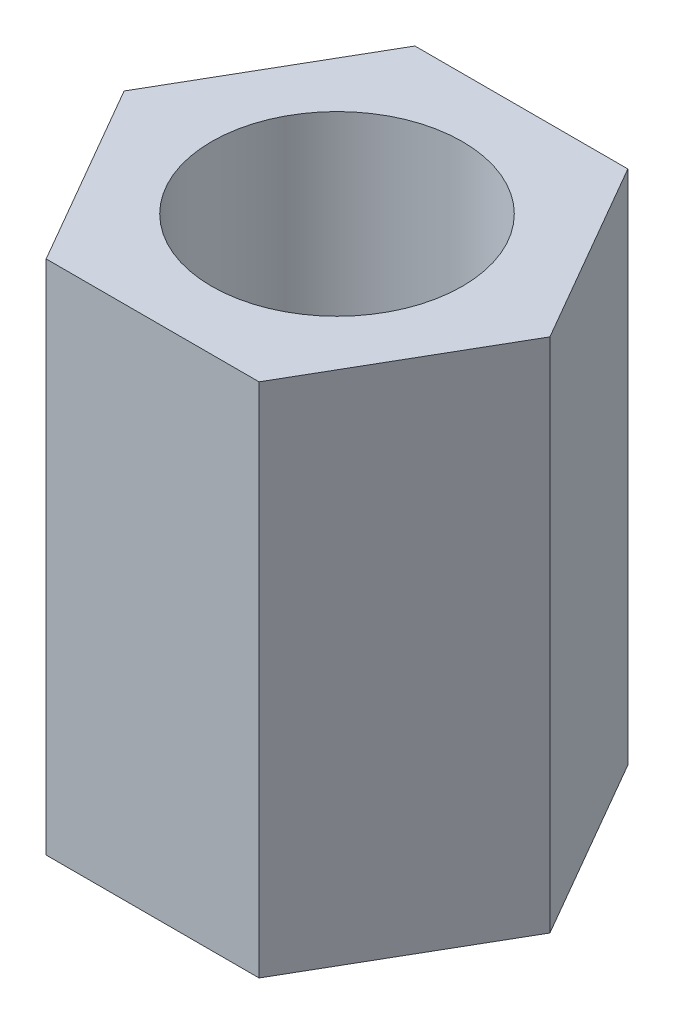
SolidWorks part; units mm, degrees
ref_plane "Front Plane" through (0, 0, 0) normal (0, 0, 1) x (1, 0, 0)
ref_plane "Top Plane" through (0, 0, 0) normal (0, 1, 0) x (1, 0, 0)
ref_plane "Right Plane" through (0, 0, 0) normal (1, 0, 0) x (0, 0, -1)
sketch "Sketch1" plane through (0, 0, 0) normal (0, 1, 0) x (1, 0, 0)
  line L1 (-2.8868, 0) -> (-1.4434, -2.5)
  line L2 (-1.4434, -2.5) -> (1.4434, -2.5)
  line L3 (1.4434, -2.5) -> (2.8868, 0)
  line L4 (2.8868, 0) -> (1.4434, 2.5)
  line L5 (1.4434, 2.5) -> (-1.4434, 2.5)
  line L6 (-1.4434, 2.5) -> (-2.8868, 0)
  circle A0 centre (0, 0) radius 1.7
  circle A1 centre (0, 0) radius 2.5 construction
  dimension "D1" = 3.4
  dimension "D2" = 5
extrude "Boss-Extrude1" add sketch "Sketch1" along normal mid plane 7
